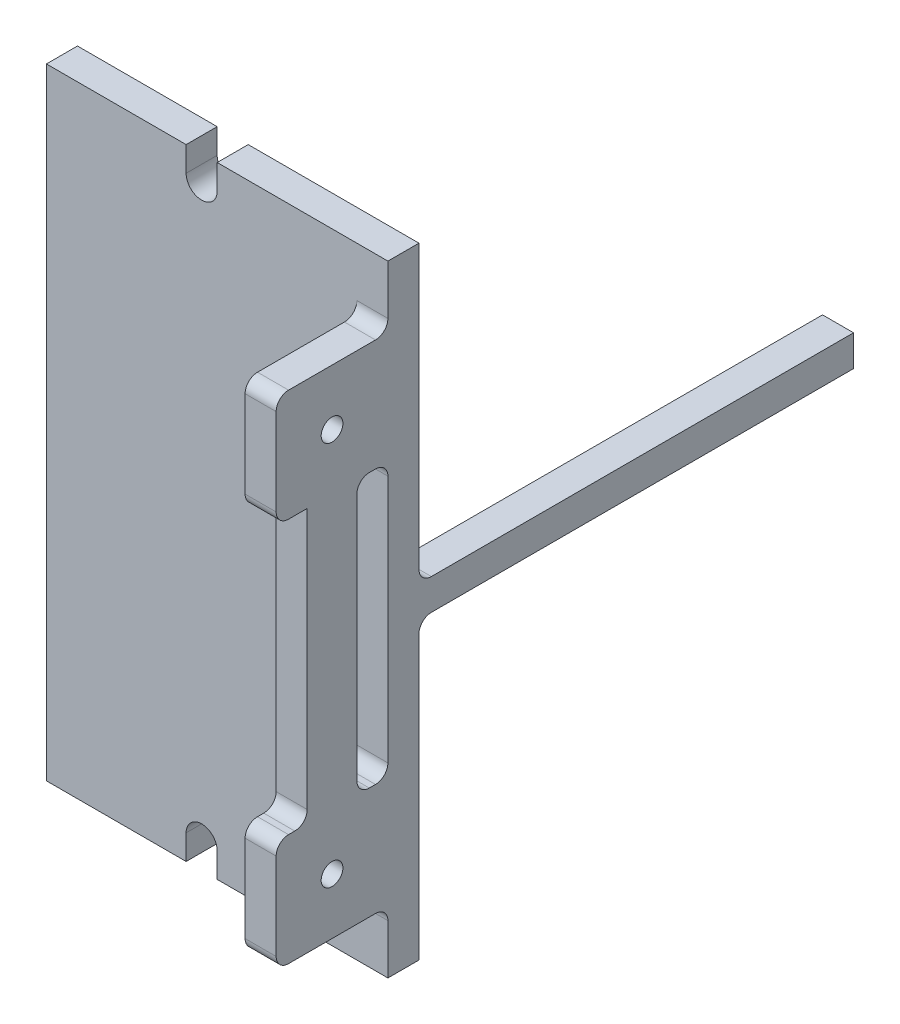
SolidWorks part; units mm, degrees
ref_plane "Front Plane" through (0, 0, 0) normal (0, 0, 1) x (1, 0, 0)
ref_plane "Top Plane" through (0, 0, 0) normal (0, 1, 0) x (1, 0, 0)
ref_plane "Right Plane" through (0, 0, 0) normal (1, 0, 0) x (0, 0, -1)
sketch "Sketch3" plane through (0, 0, 0) normal (0, 0, 1) x (1, 0, 0)
  line L0 (25, 96) -> (25, 4) construction
  line L4 (0, 100) -> (55, 100)
  line L5 (0, 100) -> (0, 0)
  line L6 (0, 0) -> (55, 0)
  line L7 (55, 100) -> (55, 0)
  line L10 (25, 0) -> (25, 4) construction
  line L11 (22.5, 0) -> (22.5, 4)
  line L12 (27.5, 0) -> (27.5, 4)
  line L13 (25, 100) -> (25, 96) construction
  line L14 (27.5, 100) -> (27.5, 96)
  line L15 (22.5, 100) -> (22.5, 96)
  arc A0 (22.5, 0) -> (27.5, 0) centre (25, 0) ccw
  arc A1 (27.5, 4) -> (22.5, 4) centre (25, 4) ccw
  arc A2 (27.5, 100) -> (22.5, 100) centre (25, 100) ccw
  arc A3 (22.5, 96) -> (27.5, 96) centre (25, 96) ccw
  point P6 (0, 0)
  point P16 (25, 2)
  point P24 (25, 98)
  dimension "D1" = 100
  dimension "D2" = 55
  dimension "D3" = 25
  dimension "D4" = 5
  dimension "D5" = 4
  dimension "D6" = 4
  dimension "D7" = 5
extrude "Boss-Extrude3" add sketch "Sketch3" along normal blind 5
sketch "Sketch4" plane through (0, 0, 0) normal (0, 0, -1) x (-1, 0, 0)
  line L0 (-55, 100) -> (-55, 0) construction
  line L1 (-55, 47.5) -> (-50, 47.5)
  line L2 (-55, 47.5) -> (-55, 52.5)
  line L3 (-55, 52.5) -> (-50, 52.5)
  line L4 (-50, 47.5) -> (-50, 52.5)
  point P4 (-55, 50)
  dimension "D1" = 5
  dimension "D2" = 5
extrude "Boss-Extrude4" add sketch "Sketch4" along normal blind 70
sketch "Sketch5" plane through (0, 0, 5) normal (0, 0, 1) x (1, 0, 0)
  line L0 (55, 50) -> (0, 50) construction
  line L1 (50, 28) -> (55, 28)
  line L2 (50, 28) -> (50, 10)
  line L3 (50, 10) -> (55, 10)
  line L4 (55, 28) -> (55, 10)
  line L5 (55, 100) -> (55, 0) construction
  line L6 (0, 100) -> (0, 0) construction
  line L7 (27.5, 0) -> (55, 0) construction
  line L8 (50, 90) -> (55, 90)
  line L9 (55, 72) -> (55, 90)
  line L10 (50, 72) -> (55, 72)
  line L11 (50, 72) -> (50, 90)
  point P12 (0, 0)
  dimension "D1" = 10
  dimension "D2" = 5
  dimension "D3" = 18
extrude "Boss-Extrude5" add sketch "Sketch5" along normal blind 18
sketch "Sketch6" plane through (50, 0, 0) normal (-1, 0, 0) x (0, 0, 1)
  line L0 (5, 19) -> (23, 19) construction
  line L1 (5, 28) -> (5, 10) construction
  line L2 (23, 28) -> (23, 10) construction
  line L3 (5, 50) -> (34.1467, 50) construction
  line L4 (5, 100) -> (5, 0) construction
  circle A0 centre (14, 19) radius 1.75
  circle A1 centre (14, 81) radius 1.75
  dimension "D1" = 3.5
extrude "Cut-Extrude1" cut sketch "Sketch6" against normal through all
sketch "Sketch7" plane through (50, 0, 0) normal (-1, 0, 0) x (0, 0, 1)
  line L0 (14, 72) -> (14, 28) construction
  line L1 (23, 72) -> (5, 72) construction
  line L2 (23, 28) -> (5, 28) construction
  line L4 (10, 72) -> (18, 72)
  line L5 (10, 72) -> (10, 28)
  line L6 (10, 28) -> (18, 28)
  line L7 (18, 72) -> (18, 28)
  line L8 (10, 72) -> (18, 28) construction
  line L9 (10, 28) -> (18, 72) construction
  point P6 (14, 50)
  dimension "D1" = 8
extrude "Boss-Extrude6" add sketch "Sketch7" against normal up to surface (5 mm away) up to face at (55, 19, 15.75)
fillet "Fillet1" radius 2 13 edges at (52.5, 52.5, 0) (52.5, 47.5, 0) (52.5, 90, 5) (52.5, 72, 5) (52.5, 10, 5) (52.5, 28, 5) (52.5, 28, 23) (52.5, 10, 23) (52.5, 90, 23) (52.5, 72, 23) (52.5, 72, 10) (52.5, 28, 10) (52.5, 28, 18)
